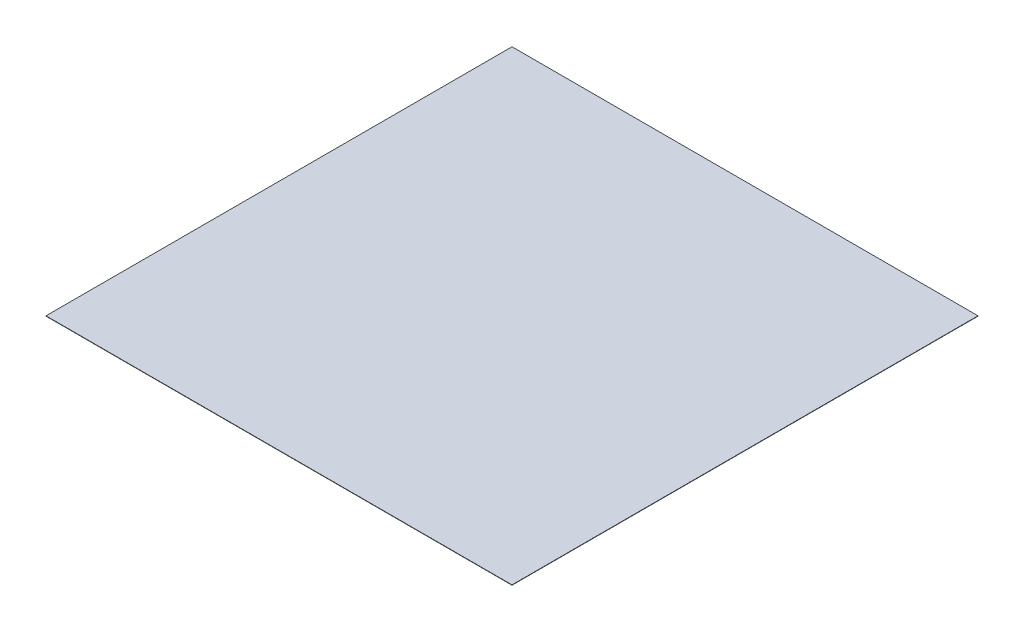
SolidWorks part; units mm, degrees
ref_plane "Front Plane" through (0, 0, 0) normal (0, 0, 1) x (1, 0, 0)
ref_plane "Top Plane" through (0, 0, 0) normal (0, 1, 0) x (1, 0, 0)
ref_plane "Right Plane" through (0, 0, 0) normal (1, 0, 0) x (0, 0, -1)
sketch "Sketch1" plane through (0, 0, 0) normal (0, 1, 0) x (1, 0, 0)
  line L1 (-47.625, -47.625) -> (47.625, -47.625)
  line L2 (-47.625, -47.625) -> (-47.625, 47.625)
  line L3 (-47.625, 47.625) -> (47.625, 47.625)
  line L4 (47.625, -47.625) -> (47.625, 47.625)
  line L5 (-47.625, -47.625) -> (47.625, 47.625) construction
  line L6 (-47.625, 47.625) -> (47.625, -47.625) construction
  point P0 (0, 0)
  dimension "D1" = 95.25
  dimension "D2" = 95.25
extrude "Boss-Extrude1" add sketch "Sketch1" along normal blind 0.065
sketch "Sketch3" plane through (0, 0.065, 0) normal (0, 1, 0) x (1, 0, 0)
  line L0 (-181.7342, -1.7772) -> (-181.7342, 178.2228) construction
